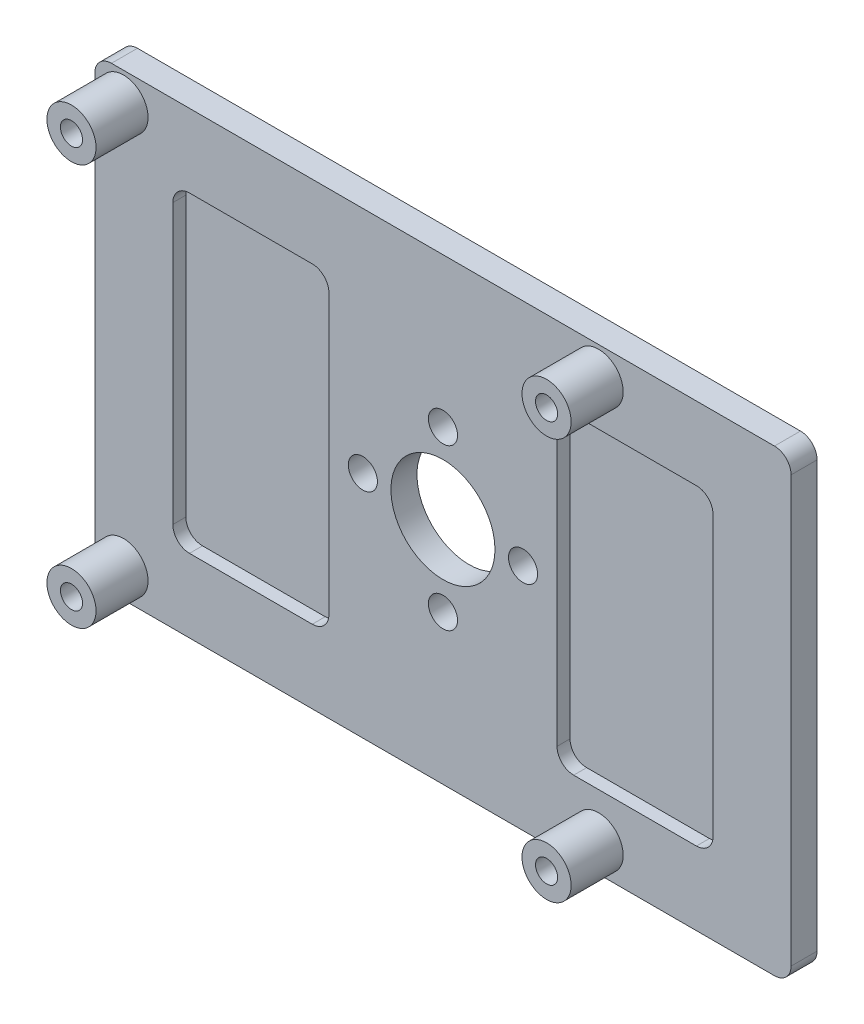
SolidWorks part; units mm, degrees
material "Copper"
ref_plane "Front Plane" through (0, 0, 0) normal (0, 0, 1) x (1, 0, 0)
ref_plane "Top Plane" through (0, 0, 0) normal (0, 1, 0) x (1, 0, 0)
ref_plane "Right Plane" through (0, 0, 0) normal (1, 0, 0) x (0, 0, -1)
sketch "Sketch1" plane through (0, 0, 0) normal (0, 0, 1) x (1, 0, 0)
  line L1 (0, 0) -> (85, 0)
  line L2 (0, 0) -> (0, 56)
  line L3 (0, 56) -> (85, 56)
  line L4 (85, 0) -> (85, 56)
  dimension "D1" = 56
  dimension "D2" = 85
extrude "Boss-Extrude1" add sketch "Sketch1" along normal blind 3.175
sketch "Sketch2" plane through (0, 0, 3.175) normal (0, 0, 1) x (1, 0, 0)
  line L0 (0, 0) -> (85, 0) construction
  line L1 (85, 0) -> (85, 56) construction
  circle A0 centre (42.5, 28) radius 6.35
  dimension "D1" = 28
  dimension "D3" = 12.7
  dimension "D2" = 42.5
extrude "Cut-Extrude1" cut sketch "Sketch2" against normal blind 3.175
sketch "Sketch3" plane through (0, 0, 3.175) normal (0, 0, 1) x (1, 0, 0)
  line L0 (0, 56) -> (0, 0) construction
  circle A0 centre (42.5, 37.779) radius 1.778
  circle A1 centre (42.5, 28) radius 6.35 construction
  dimension "D1" = 3.556
  dimension "D2" = 42.5
  dimension "D3" = 9.779
extrude "Cut-Extrude2" cut sketch "Sketch3" against normal blind 3.175
pattern_circular "CirPattern1" count 4 over 360 about axis through (42.5, 28, 0) along (0, 0, 1) of "Cut-Extrude2"
sketch "Sketch4" plane through (0, 0, 3.175) normal (0, 0, 1) x (1, 0, 0)
  line L0 (0, 56) -> (0, 0) construction
  line L1 (0, 0) -> (85, 0) construction
  line L2 (85, 56) -> (0, 56) construction
  circle A0 centre (3.5, 52.5) radius 3
  circle A2 centre (3.5, 3.5) radius 3
  circle A4 centre (61.5, 52.5) radius 3
  circle A6 centre (61.5, 3.5) radius 3
  dimension "D1" = 6
  dimension "D3" = 3.5
  dimension "D4" = 3.5
  dimension "D5" = 3.5
  dimension "D6" = 3.5
  dimension "D7" = 3.5
  dimension "D8" = 3.5
  dimension "D9" = 58
  dimension "D10" = 58
extrude "Boss-Extrude2" add sketch "Sketch4" along normal blind 6.35
sketch "Sketch6" plane through (0, 0, 3.175) normal (0, 0, 1) x (1, 0, 0)
  circle A0 centre (3.5, 3.5) radius 1.35
  circle A1 centre (61.5, 3.5) radius 1.35
  circle A2 centre (61.5, 52.5) radius 1.35
  circle A3 centre (3.5, 52.5) radius 1.35
  dimension "D1" = 2.7
extrude "Cut-Extrude3" cut sketch "Sketch6" against normal through all both and the other way through all
sketch "Sketch7" plane through (0, 0, 0) normal (0, 0, -1) x (-1, 0, 0)
  circle A0 centre (-61.5, 52.5) radius 2.159
  circle A1 centre (-3.5, 52.5) radius 2.159
  circle A2 centre (-3.5, 3.5) radius 2.159
  circle A3 centre (-61.5, 3.5) radius 2.159
  dimension "D1" = 4.318
extrude "Cut-Extrude4" cut sketch "Sketch7" against normal blind 7.025
sketch "Sketch8" plane through (0, 0, 3.175) normal (0, 0, 1) x (1, 0, 0)
  line L0 (0, 56) -> (0, 0) construction
  line L1 (9.525, 47.05) -> (28.575, 47.05)
  line L2 (9.525, 47.05) -> (9.525, 8.95)
  line L3 (9.525, 8.95) -> (28.575, 8.95)
  line L4 (28.575, 47.05) -> (28.575, 8.95)
  line L5 (56.425, 47.05) -> (75.475, 47.05)
  line L6 (56.425, 47.05) -> (56.425, 8.95)
  line L7 (56.425, 8.95) -> (75.475, 8.95)
  line L8 (75.475, 47.05) -> (75.475, 8.95)
  line L9 (85, 0) -> (85, 56) construction
  point P8 (9.525, 28)
  point P11 (0, 28)
  point P12 (75.475, 28)
  point P15 (85, 28)
  dimension "D1" = 38.1
  dimension "D2" = 19.05
  dimension "D3" = 0
  dimension "D4" = 9.525
  dimension "D5" = 19.05
  dimension "D6" = 38.1
  dimension "D7" = 0
  dimension "D8" = 9.525
extrude "Cut-Extrude5" cut sketch "Sketch8" against normal blind 1.5875
fillet "Fillet1" radius 2.032 12 edges at (9.525, 47.05, 2.3812) (28.575, 47.05, 2.3812) (28.575, 8.95, 2.3812) (9.525, 8.95, 2.3812) (75.475, 47.05, 2.3812) (56.425, 47.05, 2.3812) (75.475, 8.95, 2.3812) (56.425, 8.95, 2.3812) (0, 56, 1.5875) (85, 56, 1.5875) (85, 0, 1.5875) (0, 0, 1.5875)
